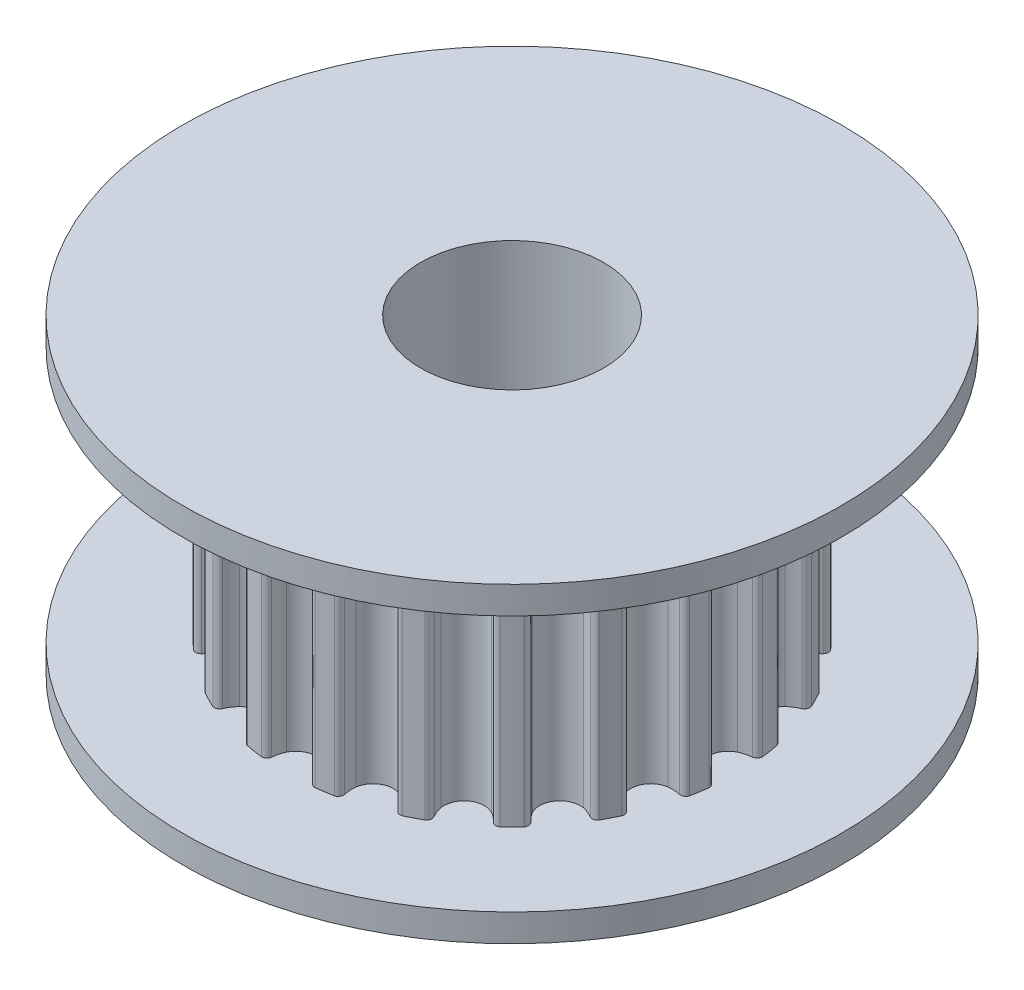
SolidWorks part; units mm, degrees
ref_plane "Front" through (0, 0, 0) normal (0, 0, 1) x (1, 0, 0)
ref_plane "Top" through (0, 0, 0) normal (0, 1, 0) x (1, 0, 0)
ref_plane "Right" through (0, 0, 0) normal (1, 0, 0) x (0, 0, -1)
sketch "Sketch1" plane through (0, 0, 0) normal (0, 0, 1) x (1, 0, 0)
  line L0 (0, 0) -> (0, 8.5) construction
  line L1 (2.5, 0) -> (2.5, 8.5)
  line L2 (2.5, 8.5) -> (9, 8.5)
  line L3 (9, 8.5) -> (9, 7.75)
  line L4 (9, 7.75) -> (6.3662, 7.75)
  line L5 (6.3662, 7.75) -> (6.3662, 0.75)
  line L6 (6.3662, 0.75) -> (9, 0.75)
  line L7 (9, 0.75) -> (9, 0)
  line L8 (9, 0) -> (2.5, 0)
  dimension "D1" = 8.5
  dimension "D2" = 7
  dimension "D3" = 18
  dimension "D4" = 12.7324
  dimension "D5" = 5
revolve "Revolve1" add sketch "Sketch1" angle 360 about L0
sketch "Sketch2" plane through (0, 0.75, 0) normal (0, 1, 0) x (1, 0, 0)
  circle A0 centre (0, 0) radius 6.3662 construction
  circle A1 centre (0, 0) radius 6.3662
  circle A3 centre (0, 0) radius 4.3662
  dimension "D1" = 2
extrude "Cut-Extrude1" cut sketch "Sketch2" along normal up to surface (7 mm away) up to face at (0, 7.75, -9)
sketch "Sketch3" plane through (0, 0.75, 0) normal (0, 1, 0) x (1, 0, 0)
  circle A0 centre (0, 0) radius 1.5
  arc A1 (6.1135, -0.7303) -> (5.9829, -0.5816) centre (5.9635, -0.7303) ccw
  arc A2 (5.659, -0.4964) -> (5.9829, -0.5816) centre (6.0717, 0.4144) ccw
  arc A3 (5.3522, 0) -> (5.659, -0.4964) centre (5.9072, 0) ccw
  arc A4 (5.659, 0.4964) -> (5.3522, 0) centre (5.9072, 0) ccw
  arc A5 (5.9829, 0.5816) -> (5.659, 0.4964) centre (6.0717, -0.4144) ccw
  arc A6 (5.9829, 0.5816) -> (6.1135, 0.7303) centre (5.9635, 0.7303) ccw
  arc A7 (6.1135, 0.7303) -> (6.0399, 1.1946) centre (0.0442, 0.007) ccw
  arc A8 (6.0399, 1.1946) -> (5.8698, 1.2957) centre (5.8973, 1.1482) ccw
  arc A9 (5.5354, 1.2766) -> (5.8698, 1.2957) centre (5.6465, 2.2704) ccw
  arc A10 (5.0902, 1.6539) -> (5.5354, 1.2766) centre (5.6181, 1.8254) ccw
  arc A11 (5.2286, 2.2208) -> (5.0902, 1.6539) centre (5.6181, 1.8254) ccw
  arc A12 (5.5103, 2.4019) -> (5.2286, 2.2208) centre (5.9026, 1.4821) ccw
  arc A13 (5.5103, 2.4019) -> (5.5886, 2.5838) centre (5.4459, 2.5374) ccw
  arc A14 (5.5886, 2.5838) -> (5.3752, 3.0025) centre (0.0399, 0.0203) ccw
  arc A15 (5.3752, 3.0025) -> (5.1821, 3.0461) centre (5.2538, 2.9144) ccw
  arc A16 (4.87, 2.9247) -> (5.1821, 3.0461) centre (4.6685, 3.9042) ccw
  arc A17 (4.33, 3.1459) -> (4.87, 2.9247) centre (4.779, 3.4722) ccw
  arc A18 (4.2864, 3.7279) -> (4.33, 3.1459) centre (4.779, 3.4722) ccw
  arc A19 (4.4984, 3.9872) -> (4.2864, 3.7279) centre (5.1557, 3.2336) ccw
  arc A20 (4.4984, 3.9872) -> (4.5166, 4.1843) centre (4.3953, 4.0961) ccw
  arc A21 (4.5166, 4.1843) -> (4.1843, 4.5166) centre (0.0317, 0.0317) ccw
  arc A22 (4.1843, 4.5166) -> (3.9872, 4.4984) centre (4.0961, 4.3953) ccw
  arc A23 (3.7279, 4.2864) -> (3.9872, 4.4984) centre (3.2336, 5.1557) ccw
  arc A24 (3.1459, 4.33) -> (3.7279, 4.2864) centre (3.4722, 4.779) ccw
  arc A25 (2.9247, 4.87) -> (3.1459, 4.33) centre (3.4722, 4.779) ccw
  arc A26 (3.0461, 5.1821) -> (2.9247, 4.87) centre (3.9042, 4.6685) ccw
  arc A27 (3.0461, 5.1821) -> (3.0025, 5.3752) centre (2.9144, 5.2538) ccw
  arc A28 (3.0025, 5.3752) -> (2.5838, 5.5886) centre (0.0203, 0.0399) ccw
  arc A29 (2.5838, 5.5886) -> (2.4019, 5.5103) centre (2.5374, 5.4459) ccw
  arc A30 (2.2208, 5.2286) -> (2.4019, 5.5103) centre (1.4821, 5.9026) ccw
  arc A31 (1.6539, 5.0902) -> (2.2208, 5.2286) centre (1.8254, 5.6181) ccw
  arc A32 (1.2766, 5.5354) -> (1.6539, 5.0902) centre (1.8254, 5.6181) ccw
  arc A33 (1.2957, 5.8698) -> (1.2766, 5.5354) centre (2.2704, 5.6465) ccw
  arc A34 (1.2957, 5.8698) -> (1.1946, 6.0399) centre (1.1482, 5.8973) ccw
  arc A35 (1.1946, 6.0399) -> (0.7303, 6.1135) centre (0.007, 0.0442) ccw
  arc A36 (0.7303, 6.1135) -> (0.5816, 5.9829) centre (0.7303, 5.9635) ccw
  arc A37 (0.4964, 5.659) -> (0.5816, 5.9829) centre (-0.4144, 6.0717) ccw
  arc A38 (0, 5.3522) -> (0.4964, 5.659) centre (0, 5.9072) ccw
  arc A39 (-0.4964, 5.659) -> (0, 5.3522) centre (0, 5.9072) ccw
  arc A40 (-0.5816, 5.9829) -> (-0.4964, 5.659) centre (0.4144, 6.0717) ccw
  arc A41 (-0.5816, 5.9829) -> (-0.7303, 6.1135) centre (-0.7303, 5.9635) ccw
  arc A42 (-0.7303, 6.1135) -> (-1.1946, 6.0399) centre (-0.007, 0.0442) ccw
  arc A43 (-1.1946, 6.0399) -> (-1.2957, 5.8698) centre (-1.1482, 5.8973) ccw
  arc A44 (-1.2766, 5.5354) -> (-1.2957, 5.8698) centre (-2.2704, 5.6465) ccw
  arc A45 (-1.6539, 5.0902) -> (-1.2766, 5.5354) centre (-1.8254, 5.6181) ccw
  arc A46 (-2.2208, 5.2286) -> (-1.6539, 5.0902) centre (-1.8254, 5.6181) ccw
  arc A47 (-2.4019, 5.5103) -> (-2.2208, 5.2286) centre (-1.4821, 5.9026) ccw
  arc A48 (-2.4019, 5.5103) -> (-2.5838, 5.5886) centre (-2.5374, 5.4459) ccw
  arc A49 (-2.5838, 5.5886) -> (-3.0025, 5.3752) centre (-0.0203, 0.0399) ccw
  arc A50 (-3.0025, 5.3752) -> (-3.0461, 5.1821) centre (-2.9144, 5.2538) ccw
  arc A51 (-2.9247, 4.87) -> (-3.0461, 5.1821) centre (-3.9042, 4.6685) ccw
  arc A52 (-3.1459, 4.33) -> (-2.9247, 4.87) centre (-3.4722, 4.779) ccw
  arc A53 (-3.7279, 4.2864) -> (-3.1459, 4.33) centre (-3.4722, 4.779) ccw
  arc A54 (-3.9872, 4.4984) -> (-3.7279, 4.2864) centre (-3.2336, 5.1557) ccw
  arc A55 (-3.9872, 4.4984) -> (-4.1843, 4.5166) centre (-4.0961, 4.3953) ccw
  arc A56 (-4.1843, 4.5166) -> (-4.5166, 4.1843) centre (-0.0317, 0.0317) ccw
  arc A57 (-4.5166, 4.1843) -> (-4.4984, 3.9872) centre (-4.3953, 4.0961) ccw
  arc A58 (-4.2864, 3.7279) -> (-4.4984, 3.9872) centre (-5.1557, 3.2336) ccw
  arc A59 (-4.33, 3.1459) -> (-4.2864, 3.7279) centre (-4.779, 3.4722) ccw
  arc A60 (-4.87, 2.9247) -> (-4.33, 3.1459) centre (-4.779, 3.4722) ccw
  arc A61 (-5.1821, 3.0461) -> (-4.87, 2.9247) centre (-4.6685, 3.9042) ccw
  arc A62 (-5.1821, 3.0461) -> (-5.3752, 3.0025) centre (-5.2538, 2.9144) ccw
  arc A63 (-5.3752, 3.0025) -> (-5.5886, 2.5838) centre (-0.0399, 0.0203) ccw
  arc A64 (-5.5886, 2.5838) -> (-5.5103, 2.4019) centre (-5.4459, 2.5374) ccw
  arc A65 (-5.2286, 2.2208) -> (-5.5103, 2.4019) centre (-5.9026, 1.4821) ccw
  arc A66 (-5.0902, 1.6539) -> (-5.2286, 2.2208) centre (-5.6181, 1.8254) ccw
  arc A67 (-5.5354, 1.2766) -> (-5.0902, 1.6539) centre (-5.6181, 1.8254) ccw
  arc A68 (-5.8698, 1.2957) -> (-5.5354, 1.2766) centre (-5.6465, 2.2704) ccw
  arc A69 (-5.8698, 1.2957) -> (-6.0399, 1.1946) centre (-5.8973, 1.1482) ccw
  arc A70 (-6.0399, 1.1946) -> (-6.1135, 0.7303) centre (-0.0442, 0.007) ccw
  arc A71 (-6.1135, 0.7303) -> (-5.9829, 0.5816) centre (-5.9635, 0.7303) ccw
  arc A72 (-5.659, 0.4964) -> (-5.9829, 0.5816) centre (-6.0717, -0.4144) ccw
  arc A73 (-5.3522, 0) -> (-5.659, 0.4964) centre (-5.9072, 0) ccw
  arc A74 (-5.659, -0.4964) -> (-5.3522, 0) centre (-5.9072, 0) ccw
  arc A75 (-5.9829, -0.5816) -> (-5.659, -0.4964) centre (-6.0717, 0.4144) ccw
  arc A76 (-5.9829, -0.5816) -> (-6.1135, -0.7303) centre (-5.9635, -0.7303) ccw
  arc A77 (-6.1135, -0.7303) -> (-6.0399, -1.1946) centre (-0.0442, -0.007) ccw
  arc A78 (-6.0399, -1.1946) -> (-5.8698, -1.2957) centre (-5.8973, -1.1482) ccw
  arc A79 (-5.5354, -1.2766) -> (-5.8698, -1.2957) centre (-5.6465, -2.2704) ccw
  arc A80 (-5.0902, -1.6539) -> (-5.5354, -1.2766) centre (-5.6181, -1.8254) ccw
  arc A81 (-5.2286, -2.2208) -> (-5.0902, -1.6539) centre (-5.6181, -1.8254) ccw
  arc A82 (-5.5103, -2.4019) -> (-5.2286, -2.2208) centre (-5.9026, -1.4821) ccw
  arc A83 (-5.5103, -2.4019) -> (-5.5886, -2.5838) centre (-5.4459, -2.5374) ccw
  arc A84 (-5.5886, -2.5838) -> (-5.3752, -3.0025) centre (-0.0399, -0.0203) ccw
  arc A85 (-5.3752, -3.0025) -> (-5.1821, -3.0461) centre (-5.2538, -2.9144) ccw
  arc A86 (-4.87, -2.9247) -> (-5.1821, -3.0461) centre (-4.6685, -3.9042) ccw
  arc A87 (-4.33, -3.1459) -> (-4.87, -2.9247) centre (-4.779, -3.4722) ccw
  arc A88 (-4.2864, -3.7279) -> (-4.33, -3.1459) centre (-4.779, -3.4722) ccw
  arc A89 (-4.4984, -3.9872) -> (-4.2864, -3.7279) centre (-5.1557, -3.2336) ccw
  arc A90 (-4.4984, -3.9872) -> (-4.5166, -4.1843) centre (-4.3953, -4.0961) ccw
  arc A91 (-4.5166, -4.1843) -> (-4.1843, -4.5166) centre (-0.0317, -0.0317) ccw
  arc A92 (-4.1843, -4.5166) -> (-3.9872, -4.4984) centre (-4.0961, -4.3953) ccw
  arc A93 (-3.7279, -4.2864) -> (-3.9872, -4.4984) centre (-3.2336, -5.1557) ccw
  arc A94 (-3.1459, -4.33) -> (-3.7279, -4.2864) centre (-3.4722, -4.779) ccw
  arc A95 (-2.9247, -4.87) -> (-3.1459, -4.33) centre (-3.4722, -4.779) ccw
  arc A96 (-3.0461, -5.1821) -> (-2.9247, -4.87) centre (-3.9042, -4.6685) ccw
  arc A97 (-3.0461, -5.1821) -> (-3.0025, -5.3752) centre (-2.9144, -5.2538) ccw
  arc A98 (-3.0025, -5.3752) -> (-2.5838, -5.5886) centre (-0.0203, -0.0399) ccw
  arc A99 (-2.5838, -5.5886) -> (-2.4019, -5.5103) centre (-2.5374, -5.4459) ccw
  arc A100 (-2.2208, -5.2286) -> (-2.4019, -5.5103) centre (-1.4821, -5.9026) ccw
  arc A101 (-1.6539, -5.0902) -> (-2.2208, -5.2286) centre (-1.8254, -5.6181) ccw
  arc A102 (-1.2766, -5.5354) -> (-1.6539, -5.0902) centre (-1.8254, -5.6181) ccw
  arc A103 (-1.2957, -5.8698) -> (-1.2766, -5.5354) centre (-2.2704, -5.6465) ccw
  arc A104 (-1.2957, -5.8698) -> (-1.1946, -6.0399) centre (-1.1482, -5.8973) ccw
  arc A105 (-1.1946, -6.0399) -> (-0.7303, -6.1135) centre (-0.007, -0.0442) ccw
  arc A106 (-0.7303, -6.1135) -> (-0.5816, -5.9829) centre (-0.7303, -5.9635) ccw
  arc A107 (-0.4964, -5.659) -> (-0.5816, -5.9829) centre (0.4144, -6.0717) ccw
  arc A108 (0, -5.3522) -> (-0.4964, -5.659) centre (0, -5.9072) ccw
  arc A109 (0.4964, -5.659) -> (0, -5.3522) centre (0, -5.9072) ccw
  arc A110 (0.5816, -5.9829) -> (0.4964, -5.659) centre (-0.4144, -6.0717) ccw
  arc A111 (0.5816, -5.9829) -> (0.7303, -6.1135) centre (0.7303, -5.9635) ccw
  arc A112 (0.7303, -6.1135) -> (1.1946, -6.0399) centre (0.007, -0.0442) ccw
  arc A113 (1.1946, -6.0399) -> (1.2957, -5.8698) centre (1.1482, -5.8973) ccw
  arc A114 (1.2766, -5.5354) -> (1.2957, -5.8698) centre (2.2704, -5.6465) ccw
  arc A115 (1.6539, -5.0902) -> (1.2766, -5.5354) centre (1.8254, -5.6181) ccw
  arc A116 (2.2208, -5.2286) -> (1.6539, -5.0902) centre (1.8254, -5.6181) ccw
  arc A117 (2.4019, -5.5103) -> (2.2208, -5.2286) centre (1.4821, -5.9026) ccw
  arc A118 (2.4019, -5.5103) -> (2.5838, -5.5886) centre (2.5374, -5.4459) ccw
  arc A119 (2.5838, -5.5886) -> (3.0025, -5.3752) centre (0.0203, -0.0399) ccw
  arc A120 (3.0025, -5.3752) -> (3.0461, -5.1821) centre (2.9144, -5.2538) ccw
  arc A121 (2.9247, -4.87) -> (3.0461, -5.1821) centre (3.9042, -4.6685) ccw
  arc A122 (3.1459, -4.33) -> (2.9247, -4.87) centre (3.4722, -4.779) ccw
  arc A123 (3.7279, -4.2864) -> (3.1459, -4.33) centre (3.4722, -4.779) ccw
  arc A124 (3.9872, -4.4984) -> (3.7279, -4.2864) centre (3.2336, -5.1557) ccw
  arc A125 (3.9872, -4.4984) -> (4.1843, -4.5166) centre (4.0961, -4.3953) ccw
  arc A126 (4.1843, -4.5166) -> (4.5166, -4.1843) centre (0.0317, -0.0317) ccw
  arc A127 (4.5166, -4.1843) -> (4.4984, -3.9872) centre (4.3953, -4.0961) ccw
  arc A128 (4.2864, -3.7279) -> (4.4984, -3.9872) centre (5.1557, -3.2336) ccw
  arc A129 (4.33, -3.1459) -> (4.2864, -3.7279) centre (4.779, -3.4722) ccw
  arc A130 (4.87, -2.9247) -> (4.33, -3.1459) centre (4.779, -3.4722) ccw
  arc A131 (5.1821, -3.0461) -> (4.87, -2.9247) centre (4.6685, -3.9042) ccw
  arc A132 (5.1821, -3.0461) -> (5.3752, -3.0025) centre (5.2538, -2.9144) ccw
  arc A133 (5.3752, -3.0025) -> (5.5886, -2.5838) centre (0.0399, -0.0203) ccw
  arc A134 (5.5886, -2.5838) -> (5.5103, -2.4019) centre (5.4459, -2.5374) ccw
  arc A135 (5.2286, -2.2208) -> (5.5103, -2.4019) centre (5.9026, -1.4821) ccw
  arc A136 (5.0902, -1.6539) -> (5.2286, -2.2208) centre (5.6181, -1.8254) ccw
  arc A137 (5.5354, -1.2766) -> (5.0902, -1.6539) centre (5.6181, -1.8254) ccw
  arc A138 (5.8698, -1.2957) -> (5.5354, -1.2766) centre (5.6465, -2.2704) ccw
  arc A139 (5.8698, -1.2957) -> (6.0399, -1.1946) centre (5.8973, -1.1482) ccw
  arc A140 (6.0399, -1.1946) -> (6.1135, -0.7303) centre (0.0442, -0.007) ccw
  circle A141 centre (0, 0) radius 4.3662 construction
  circle A142 centre (0, 0) radius 4.3662
extrude "Boss-Extrude1" add sketch "Sketch3" along normal up to surface (7 mm away) contours A139 A140 A1 A2 A3 A4 A5 A6 A7 A8 A9 A10 A11 A12 A13 A14 A15 A16 A17 A18 A19 A20 A21 A22 A23 A24 A25 A26 A27 A28 A29 A30 A31 A32 A33 A34 A35 A36 A37 A38 A39 A40 A41 A42 A43 A44 A45 A46 A47 A48 A49
sketch "innermost_diameter" plane through (0, 7.75, 0) normal (0, -1, 0) x (1, 0, 0)
  circle A0 centre (0, 0) radius 5.3522
  point P0 (0, 0)
equation "\"D4@Sketch1\"=20*2/3.14159"
